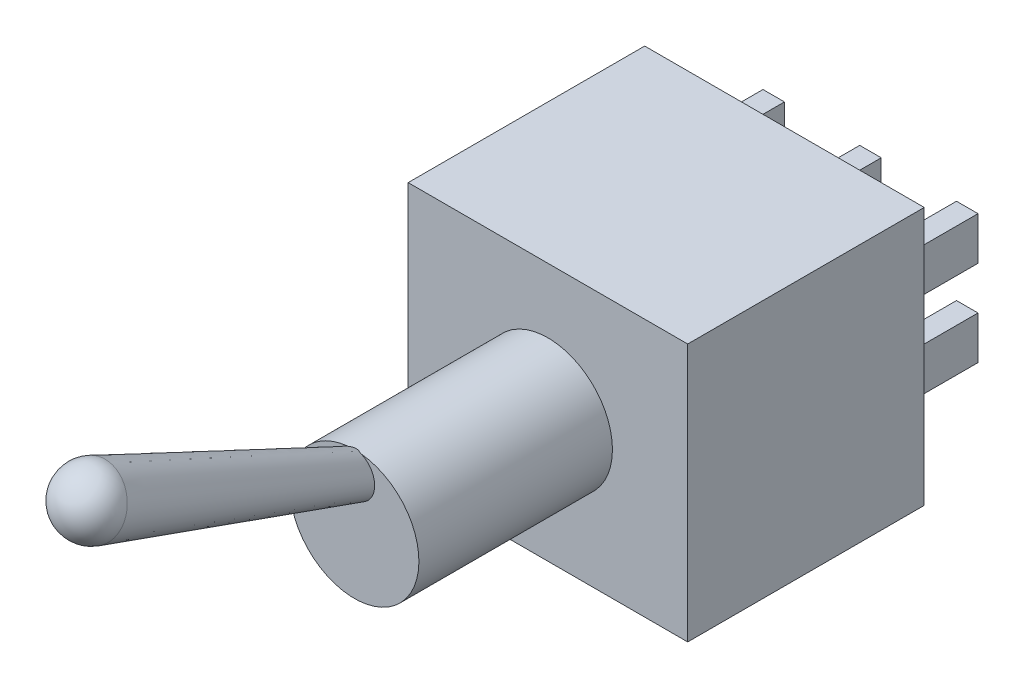
SolidWorks part; units mm, degrees
ref_plane "Front Plane" through (0, 0, 0) normal (1, 0, 0) x (0, 1, 0)
ref_plane "Top Plane" through (0, 0, 0) normal (0, 0, 1) x (0, 1, 0)
ref_plane "Right Plane" through (0, 0, 0) normal (0, 1, 0) x (-1, 0, 0)
sketch "Sketch1" plane through (0, 0, 0) normal (0, 0, 1) x (0, 1, 0)
  line L1 (0, 0) -> (12, 0)
  line L2 (0, 0) -> (0, 13)
  line L3 (0, 13) -> (12, 13)
  line L4 (12, 0) -> (12, 13)
  dimension "D1" = 13
  dimension "D2" = 12
extrude "Boss-Extrude1" add sketch "Sketch1" along normal blind 11
sketch "Sketch2" plane through (0, 0, 0) normal (0, 0, 1) x (0, 1, 0)
  line L0 (12, 13) -> (0, 13) construction
  line L1 (3, 7) -> (5, 7)
  line L2 (3, 7) -> (3, 6)
  line L3 (3, 6) -> (5, 6)
  line L4 (5, 7) -> (5, 6)
  line L5 (7, 7) -> (9, 7)
  line L6 (7, 7) -> (7, 6)
  line L7 (7, 6) -> (9, 6)
  line L8 (9, 7) -> (9, 6)
  line L9 (3, 11.5) -> (5, 11.5)
  line L10 (3, 11.5) -> (3, 10.5)
  line L11 (3, 10.5) -> (5, 10.5)
  line L12 (5, 11.5) -> (5, 10.5)
  line L13 (7, 11.5) -> (9, 11.5)
  line L14 (7, 11.5) -> (7, 10.5)
  line L15 (7, 10.5) -> (9, 10.5)
  line L16 (9, 11.5) -> (9, 10.5)
  line L17 (3, 2.5) -> (5, 2.5)
  line L18 (3, 2.5) -> (3, 1.5)
  line L19 (3, 1.5) -> (5, 1.5)
  line L20 (5, 2.5) -> (5, 1.5)
  line L21 (7, 2.5) -> (9, 2.5)
  line L22 (7, 2.5) -> (7, 1.5)
  line L23 (7, 1.5) -> (9, 1.5)
  line L24 (9, 2.5) -> (9, 1.5)
  line L25 (0, 13) -> (0, 0) construction
  line L26 (12, 0) -> (12, 13) construction
  line L27 (0, 0) -> (12, 0) construction
  point P24 (7, 2)
  dimension "D1" = 1
  dimension "D2" = 2
  dimension "D3" = 1.5
  dimension "D4" = 1.5
  dimension "D5" = 3
  dimension "D6" = 3
  dimension "D7" = 1.5
  dimension "D8" = 1.5
  dimension "D9" = 3
  dimension "D10" = 3
  dimension "D11" = 3
  dimension "D12" = 3
  dimension "D13" = 6
  dimension "D14" = 6
extrude "Boss-Extrude2" add sketch "Sketch2" against normal blind 4
sketch "Sketch3" plane through (0, 0, 11) normal (0, 0, 1) x (1, 0, 0)
  line L0 (-13, 0) -> (0, 0) construction
  line L2 (-13, 12) -> (-13, 0) construction
  circle A0 centre (-6.5, 6) radius 3
  dimension "D1" = 6
  dimension "D3" = 6
  dimension "D2" = 6.5
extrude "Boss-Extrude3" add sketch "Sketch3" along normal blind 9
ref_plane "Plane1" through (-6.5, 0, 0) normal (1, 0, 0) x (0, 1, 0)
sketch "Sketch4" plane through (-6.5, 0, 0) normal (1, 0, 0) x (0, 1, 0)
  line L0 (7, 20) -> (11.6372, 32.7406)
  line L1 (9, 20) -> (3, 20) construction
  line L3 (8, 20) -> (13.6207, 33.6133) construction
  line L4 (13.6207, 33.6133) -> (8, 20)
  line L5 (7, 20) -> (8, 20)
  arc A0 (11.6372, 32.7406) -> (13.6207, 33.6133) centre (13.0467, 32.2275) cw
  dimension "D5" = 1.5
  dimension "D1" = 110
  dimension "D3" = 7
revolve "Revolve1" add sketch "Sketch4" angle 360 about L3
